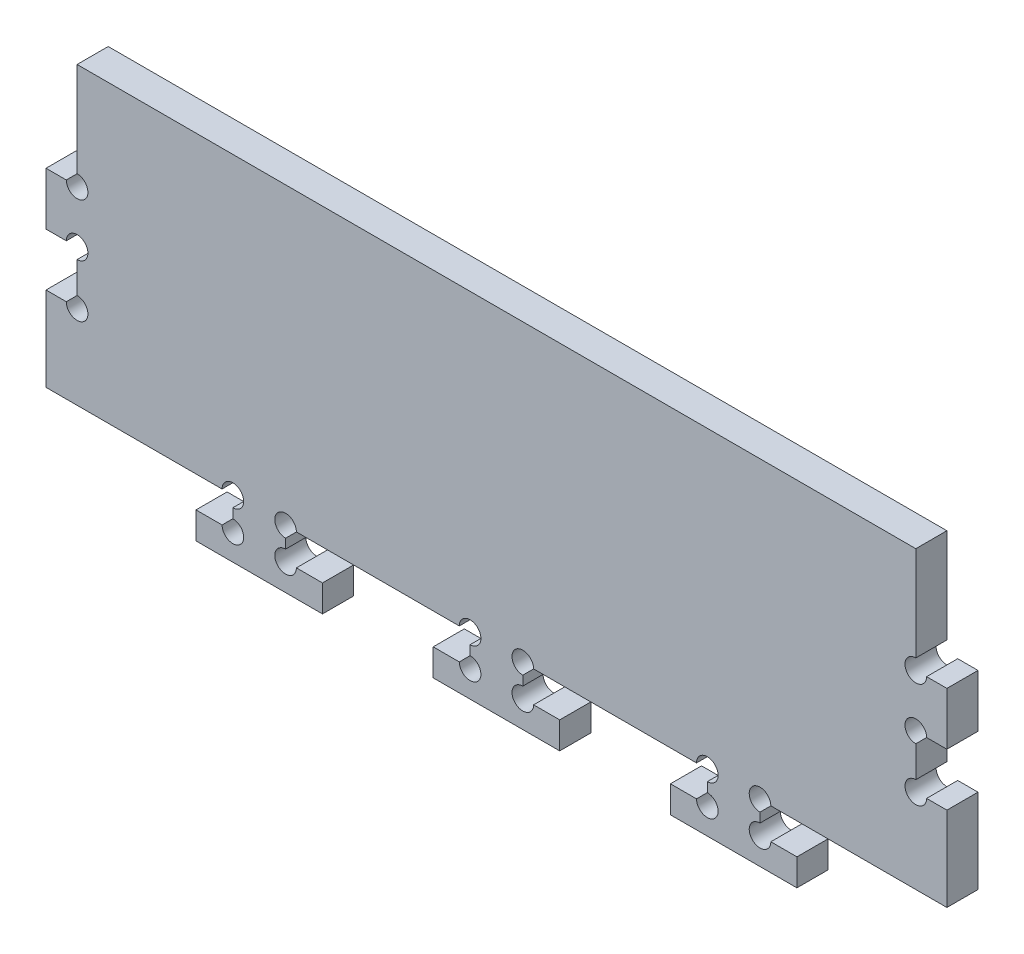
SolidWorks part; units mm, degrees
ref_plane "Front Plane" through (0, 0, 0) normal (0, 0, 1) x (1, 0, 0)
ref_plane "Top Plane" through (0, 0, 0) normal (0, 1, 0) x (1, 0, 0)
ref_plane "Right Plane" through (0, 0, 0) normal (1, 0, 0) x (0, 0, -1)
sketch "Sketch1" plane through (0, 0, 0) normal (0, 0, 1) x (1, 0, 0)
  line L1 (85.45, -35) -> (-85.45, -35)
  line L2 (85.45, -35) -> (85.45, 35)
  line L3 (85.45, 35) -> (-85.45, 35)
  line L4 (-85.45, -35) -> (-85.45, 35)
  line L5 (85.45, -35) -> (-85.45, 35) construction
  line L6 (85.45, 35) -> (-85.45, -35) construction
  point P0 (0, 0)
  dimension "D1" = 170.9
  dimension "D2" = 70
extrude "Boss-Extrude1" add sketch "Sketch1" along normal blind 5.9
sketch "Sketch2" plane through (0, 0, 5.9) normal (0, 0, 1) x (1, 0, 0)
  line L0 (-85.45, 35) -> (-85.45, -35) construction
  line L1 (-85.45, -21) -> (85.45, -21)
  line L2 (-85.45, -21) -> (-85.45, -35)
  line L3 (-85.45, -35) -> (85.45, -35)
  line L4 (85.45, -21) -> (85.45, -35)
  line L5 (-50, -21) -> (-50, -26.9)
  line L6 (-50, -26.9) -> (-57, -26.9)
  line L7 (-57, -26.9) -> (-57, -32)
  line L8 (-57, -32) -> (-33, -32)
  line L9 (-33, -32) -> (-33, -26.9)
  line L10 (-33, -26.9) -> (-40, -26.9)
  line L11 (-40, -26.9) -> (-40, -21)
  line L12 (-40, -21) -> (-50, -21)
  line L13 (-50, -26.9) -> (-40, -26.9) construction
  line L14 (-5, -26.9) -> (5, -26.9) construction
  line L16 (-5, -21) -> (-5, -26.9)
  line L17 (-12, -26.9) -> (-12, -32)
  line L18 (-12, -32) -> (12, -32)
  line L19 (12, -32) -> (12, -26.9)
  line L20 (12, -26.9) -> (5, -26.9)
  line L21 (5, -26.9) -> (5, -21)
  line L22 (-5, -26.9) -> (-12, -26.9)
  line L23 (40, -21) -> (40, -26.9)
  line L24 (33, -26.9) -> (33, -32)
  line L25 (33, -32) -> (57, -32)
  line L26 (57, -32) -> (57, -26.9)
  line L27 (57, -26.9) -> (50, -26.9)
  line L28 (50, -26.9) -> (50, -21)
  line L29 (40, -26.9) -> (33, -26.9)
  point P9 (-45, -26.9)
  point P16 (-45, -32)
  point P17 (0, -26.9)
  point P22 (-5, -23.95)
  line M23 (-85.45, 35) -> (-85.45, -35)
  line M24 (-85.45, -35) -> (85.45, -35)
  line M25 (85.45, -35) -> (85.45, 35)
  dimension "D1" = 14
  dimension "D2" = 10
  dimension "D3" = 5.9
  dimension "D5" = 24
  dimension "D7" = 35
  dimension "D4" = 5.1
  dimension "D6" = 3
extrude "Cut-Extrude1" cut sketch "Sketch2" against normal through all contours L29 L23 L1 L21 L20 L19 L18 L17 L22 L16 L11 L10 L9 L8 L7 L6 L5 L28 L27 L26 L25 L24 M23 M24 M25
sketch "Sketch3" plane through (0, 0, 5.9) normal (0, 0, 1) x (1, 0, 0)
  line L0 (85.45, -21) -> (85.45, 35) construction
  line L1 (85.45, 25) -> (79.55, 25)
  line L2 (85.45, 25) -> (85.45, 15)
  line L3 (85.45, 15) -> (79.55, 15)
  line L4 (79.55, 25) -> (79.55, 15)
  line L5 (79.55, 15) -> (79.55, 5) construction
  line L6 (85.45, 5) -> (79.55, 5)
  line L7 (85.45, 5) -> (85.45, -5)
  line L8 (85.45, -5) -> (79.55, -5)
  line L9 (79.55, 5) -> (79.55, -5)
  line L10 (85.45, 35) -> (-85.45, 35) construction
  line L11 (0, 0) -> (0, 32.6921) construction
  line L12 (-79.55, 15) -> (-79.55, 5) construction
  line L13 (-79.55, 5) -> (-79.55, -5)
  line L14 (-85.45, -5) -> (-79.55, -5)
  line L15 (-85.45, 5) -> (-85.45, -5)
  line L16 (-85.45, 5) -> (-79.55, 5)
  line L17 (-79.55, 25) -> (-79.55, 15)
  line L18 (-85.45, 15) -> (-79.55, 15)
  line L19 (-85.45, 25) -> (-85.45, 15)
  line L20 (-85.45, 25) -> (-79.55, 25)
  dimension "D1" = 10
  dimension "D2" = 5.9
  dimension "D3" = 10
  dimension "D4" = 10
extrude "Cut-Extrude2" cut sketch "Sketch3" against normal through all
sketch "Sketch4" plane through (0, 0, 5.9) normal (0, 0, 1) x (1, 0, 0)
  line L1 (79.55, 25) -> (85.45, 25)
  line L2 (79.55, 25) -> (79.55, 35)
  line L3 (79.55, 35) -> (85.45, 35)
  line L4 (85.45, 25) -> (85.45, 35)
  line L9 (0, 0) -> (0, 20.4022) construction
  line L10 (-85.45, 25) -> (-85.45, 35)
  line L11 (-79.55, 35) -> (-85.45, 35)
  line L12 (-79.55, 25) -> (-79.55, 35)
  line L13 (-79.55, 25) -> (-85.45, 25)
extrude "Cut-Extrude3" cut sketch "Sketch4" against normal through all
sketch "Sketch5" plane through (0, 0, 5.9) normal (0, 0, 1) x (1, 0, 0)
  circle A0 centre (-50, -26.9) radius 2.05
  circle A1 centre (-40, -26.9) radius 2.05
  circle A2 centre (-50, -21) radius 2.05
  circle A3 centre (-40, -21) radius 2.05
  circle A4 centre (-5, -21) radius 2.05
  circle A5 centre (5, -21) radius 2.05
  circle A6 centre (-5, -26.9) radius 2.05
  circle A7 centre (5, -26.9) radius 2.05
  circle A8 centre (40, -26.9) radius 2.05
  circle A9 centre (50, -26.9) radius 2.05
  circle A10 centre (50, -21) radius 2.05
  circle A11 centre (40, -21) radius 2.05
  circle A12 centre (79.55, -5) radius 2.05
  circle A13 centre (79.55, 5) radius 2.05
  circle A14 centre (79.55, 15) radius 2.05
  circle A15 centre (-79.55, 15) radius 2.05
  circle A16 centre (-79.55, 5) radius 2.05
  circle A17 centre (-79.55, -5) radius 2.05
  dimension "D1" = 4.1
extrude "Cut-Extrude4" cut sketch "Sketch5" against normal up to next
equation "\"e\" = 5.9"
equation "\"D1@Boss-Extrude1\"=\"e\""
equation "\"D3@Sketch2\"= \"e\""
equation "\"D1@Sketch1\"= 165 + \"e\""
equation "\"D2@Sketch3\"= \"e\""
